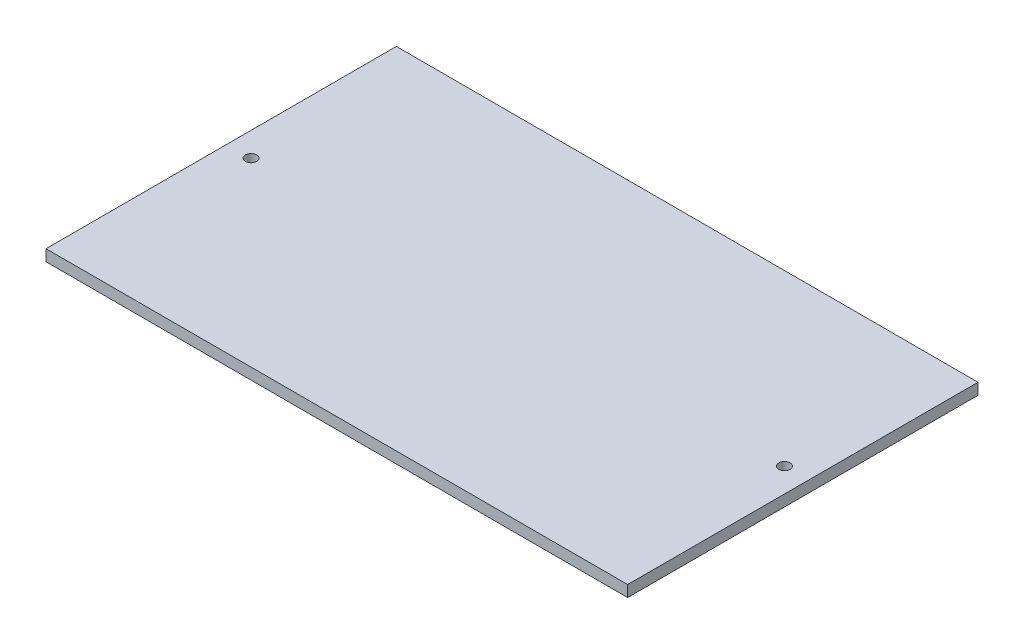
SolidWorks part; units mm, degrees
ref_plane "Front Plane" through (0, 0, 0) normal (0, 0, 1) x (1, 0, 0)
ref_plane "Top Plane" through (0, 0, 0) normal (0, 1, 0) x (1, 0, 0)
ref_plane "Right Plane" through (0, 0, 0) normal (1, 0, 0) x (0, 0, -1)
sketch "Sketch1" plane through (0, 0, 0) normal (0, 1, 0) x (1, 0, 0)
  line L1 (-51.5, -31.02) -> (51.5, -31.02)
  line L2 (-51.5, -31.02) -> (-51.5, 31.02)
  line L3 (-51.5, 31.02) -> (51.5, 31.02)
  line L4 (51.5, -31.02) -> (51.5, 31.02)
  line L5 (-51.5, -31.02) -> (51.5, 31.02) construction
  line L6 (-51.5, 31.02) -> (51.5, -31.02) construction
  circle A0 centre (47.23, 1.02) radius 1
  circle A1 centre (-47.23, 1.02) radius 1
  point P0 (0, 0)
  dimension "D5" = 2
  dimension "D6" = 2
  dimension "D1" = 62.04
  dimension "D2" = 103
  dimension "D3" = 4.27
  dimension "D4" = 30
  dimension "D7" = 30
  dimension "D8" = 4.27
extrude "Boss-Extrude1" add sketch "Sketch1" along normal blind 2
